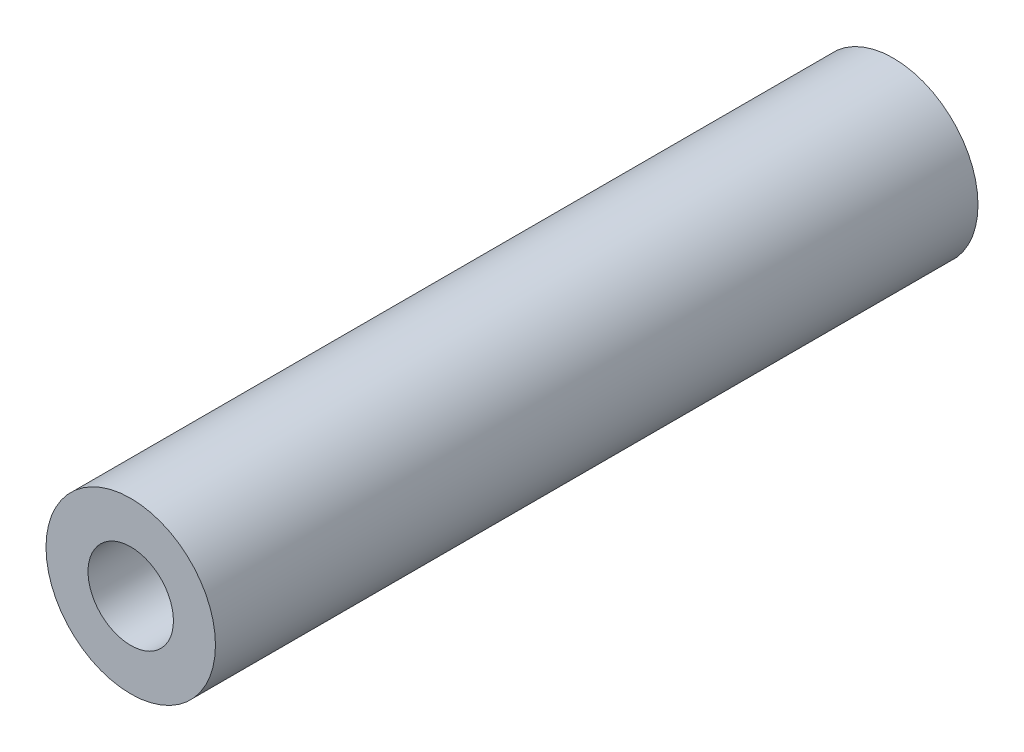
SolidWorks part; units mm, degrees
ref_plane "Front Plane" through (0, 0, 0) normal (0, 0, 1) x (1, 0, 0)
ref_plane "Top Plane" through (0, 0, 0) normal (0, 1, 0) x (1, 0, 0)
ref_plane "Right Plane" through (0, 0, 0) normal (1, 0, 0) x (0, 0, -1)
sketch "Sketch1" plane through (0, 0, 0) normal (0, 0, 1) x (1, 0, 0)
  circle A0 centre (0, 0) radius 6.35
  circle A1 centre (0, 0) radius 3.2004
  dimension "OD" = 12.7
  dimension "ID" = 6.4008
extrude "Extrude1" add sketch "Sketch1" along normal mid plane 57.15
sketch "Sketch2" plane through (0, 0, 0) normal (1, 0, 0) x (0, 0, -1)
  line L0 (-28.575, -3.2004) -> (28.575, -3.2004) construction
  line L3 (28.575, 3.2004) -> (-28.575, 3.2004) construction
  line L5 (-28.575, -3.2004) -> (28.575, -3.2004)
  line L6 (28.575, 3.2004) -> (-28.575, 3.2004)
sketch "Sketch4" plane through (0, 0, 28.575) normal (0, 0, 1) x (1, 0, 0)
  line L0 (0, 0) -> (-2.263, 2.263)
  line L1 (0, -3.4925) -> (0, 3.4925) construction
  circle A0 centre (0, 0) radius 3.2004 construction
  dimension "D1" = 45
